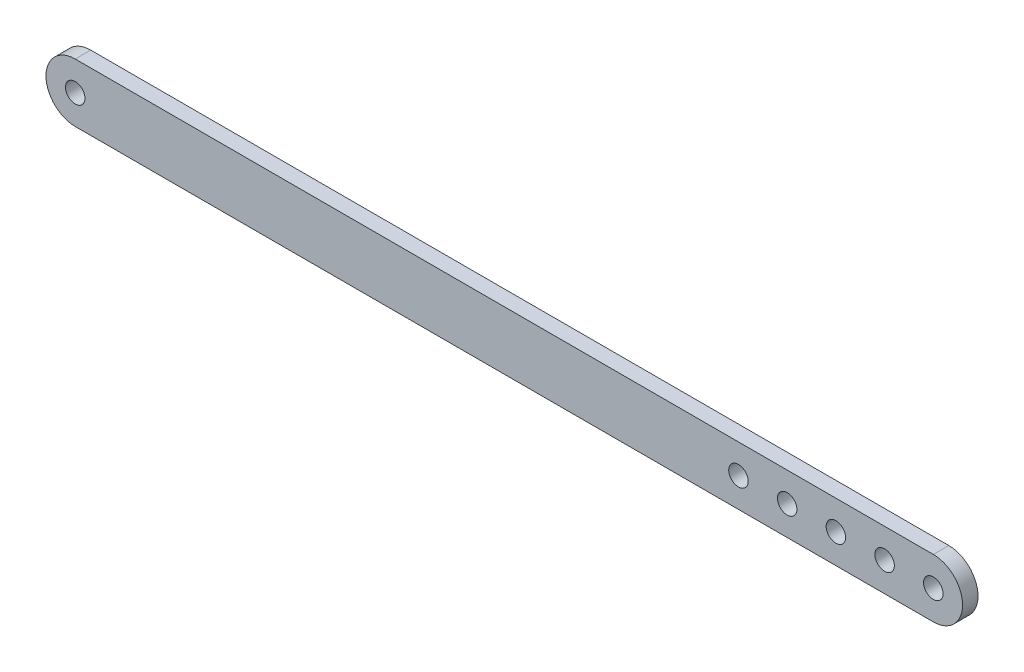
SolidWorks part; units mm, degrees
ref_plane "Front Plane" through (0, 0, 0) normal (0, 0, 1) x (1, 0, 0)
ref_plane "Top Plane" through (0, 0, 0) normal (0, 1, 0) x (1, 0, 0)
ref_plane "Right Plane" through (0, 0, 0) normal (1, 0, 0) x (0, 0, -1)
sketch "Sketch1" plane through (0, 0, 0) normal (0, 0, 1) x (1, 0, 0)
  line L0 (0, 6) -> (176.1626, 6)
  line L1 (176.1626, -6) -> (0, -6)
  line L2 (176.1626, 0) -> (166.1626, 0) construction
  circle A0 centre (0, 0) radius 2
  arc A1 (0, 6) -> (0, -6) centre (0, 0) ccw
  arc A2 (176.1626, 6) -> (176.1626, -6) centre (176.1626, 0) cw
  circle A3 centre (176.1626, 0) radius 2
  circle A4 centre (166.1626, 0) radius 2
  circle A5 centre (156.1626, 0) radius 2
  circle A6 centre (146.1626, 0) radius 2
  circle A7 centre (136.1626, 0) radius 2
  dimension "D1" = 4
  dimension "D3" = 10
  dimension "D4" = 156.1626
  dimension "D5" = 12
  dimension "D2" = 5
extrude "Boss-Extrude1" add sketch "Sketch1" along normal blind 3.175
